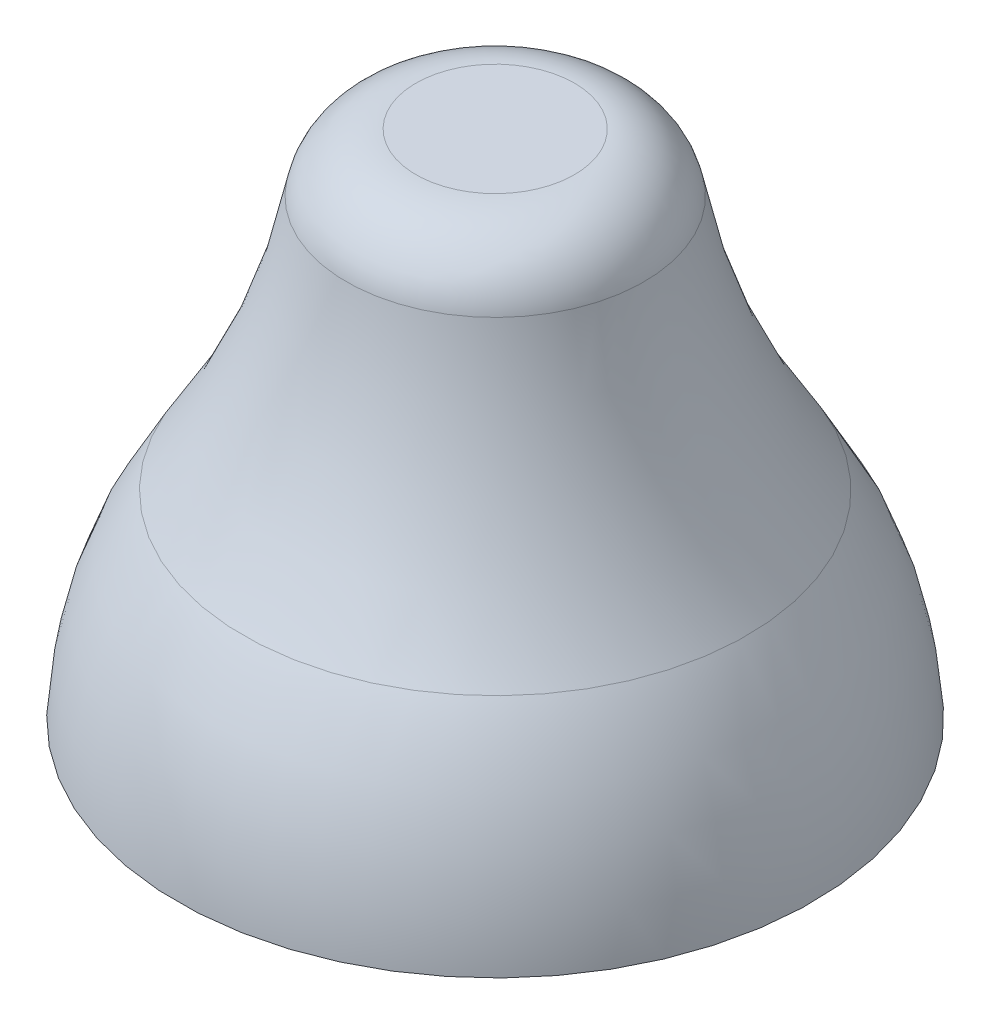
SolidWorks part; units mm, degrees
ref_plane "Front Plane" through (0, 0, 0) normal (0, 0, 1) x (1, 0, 0)
ref_plane "Top Plane" through (0, 0, 0) normal (0, 1, 0) x (1, 0, 0)
ref_plane "Right Plane" through (0, 0, 0) normal (1, 0, 0) x (0, 0, -1)
sketch "Sketch1" plane through (0, 0, 0) normal (0, 0, 1) x (1, 0, 0)
  line L0 (0, 0) -> (0.9, 0)
  line L1 (0, 0) -> (0, 1.45)
  line L2 (0, 1.45) -> (0.225, 1.45)
  arc A0 (0.9, 0) -> (0.714, 0.562) centre (-0.1988, -0.0519) ccw
  arc A1 (0.714, 0.562) -> (0.4219, 1.285) centre (2.2921, 1.6201) cw
  arc A2 (0.4219, 1.285) -> (0.225, 1.45) centre (0.225, 1.25) ccw
  dimension "D3" = 0.2
  dimension "D4" = 1.1
  dimension "D5" = 1.9
  dimension "D1" = 1.45
  dimension "D2" = 0.9
  dimension "D6" = 0.225
  dimension "D7" = 0.2
  dimension "D8" = 0.165
  dimension "D9" = 0.888
  dimension "D10" = 0.714
revolve "Revolve1" add sketch "Sketch1" angle 360 about L1
